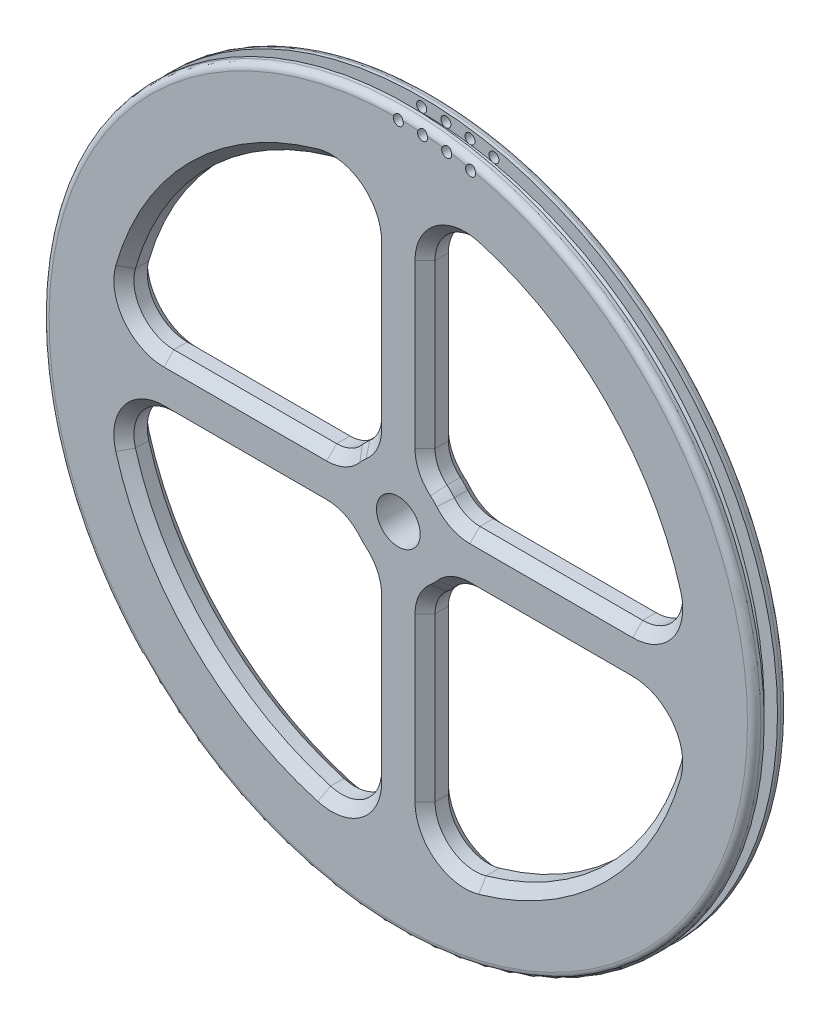
SolidWorks part; units mm, degrees
ref_plane "Front Plane" through (0, 0, 0) normal (0, 0, 1) x (1, 0, 0)
ref_plane "Top Plane" through (0, 0, 0) normal (0, 1, 0) x (1, 0, 0)
ref_plane "Right Plane" through (0, 0, 0) normal (1, 0, 0) x (0, 0, -1)
sketch "Sketch2" plane through (0, 0, 0) normal (0, 0, 1) x (1, 0, 0)
  circle A0 centre (0, 0) radius 50.8
  dimension "D1" = 101.6
extrude "Boss-Extrude2" add sketch "Sketch2" along normal blind 2
sketch "Sketch3" plane through (0, 0, 2) normal (0, 0, 1) x (1, 0, 0)
  circle A2 centre (0, 0) radius 53.3
  circle A3 centre (0, 0) radius 53.3
  dimension "D1" = 2.5
extrude "Boss-Extrude3" add sketch "Sketch3" along normal blind 1.5
ref_plane "Plane1" through (0, 0, 1) normal (0, 0, -1) x (-1, 0, 0)
mirror "Mirror2" about plane through (0, 0, 1) normal (0, 0, -1) of "Boss-Extrude3"
chamfer "Chamfer1" distance 0.5 angle 45 2 edges at (50.8, 0, 0) (50.8, 0, 2)
sketch "Sketch4" plane through (0, 0, -1.5) normal (0, 0, -1) x (-1, 0, 0)
  line L0 (0, 0) -> (0, 4)
  line L1 (0, 0) -> (4, 0)
  line L2 (0, 0) -> (0, -4)
  line L3 (0, 0) -> (-4, 0)
  line L6 (8.0623, -4) -> (42.5, -4)
  line L7 (-4, -8.0623) -> (-4, -42.5)
  line L8 (-8.0623, -4) -> (-42.5, -4)
  line L11 (4, -8.0623) -> (4, -42.5)
  line L12 (0, 0) -> (-42.5, 0) construction
  line L13 (-8.0623, 4) -> (-42.5, 4)
  line L15 (-4, 8.0623) -> (-4, 42.5)
  line L19 (4, 8.0623) -> (4, 42.5)
  line L21 (8.0623, 4) -> (42.5, 4)
  line L24 (0, 0) -> (42.5, 0) construction
  line L25 (4, 0) -> (4, -42.5) construction
  line L26 (0, -4) -> (42.5, -4) construction
  line L28 (0, 0) -> (0, -42.5) construction
  line L29 (0, -4) -> (-42.5, -4) construction
  line L30 (-4, 0) -> (-4, -42.5) construction
  circle A0 centre (0, 0) radius 3.275
  arc A1 (-8.0623, -4) -> (-4, -8.0623) centre (0, 0) ccw
  arc A2 (-42.3113, -4) -> (-4, -42.3113) centre (0, 0) ccw
  arc A3 (4, -8.0623) -> (8.0623, -4) centre (0, 0) ccw
  arc A4 (8.0623, 4) -> (4, 8.0623) centre (0, 0) ccw
  arc A5 (-4, 8.0623) -> (-8.0623, 4) centre (0, 0) ccw
  arc A6 (42.3113, 4) -> (4, 42.3113) centre (0, 0) ccw
  arc A7 (4, -42.3113) -> (42.3113, -4) centre (0, 0) ccw
  arc A8 (-4, 42.3113) -> (-42.3113, 4) centre (0, 0) ccw
  dimension "D1" = 6.55
  dimension "D2" = 18
  dimension "D3" = 85
  dimension "D4" = 4
  dimension "D5" = 4
extrude "Cut-Extrude1" cut sketch "Sketch4" against normal through all contours L15 A8 L13 A5 | L21 A6 L19 A4 | L11 A7 L6 A3 | L8 A2 L7 A1 | L2 A0 L1 | L1 A0 L0 | L0 A0 L3 | L3 A0 L2
fillet "Fillet1" radius 6 8 edges at (-4, 42.3113, 1) (-42.3113, 4, 1) (-42.3113, -4, 1) (-4, -42.3113, 1) (4, -42.3113, 1) (42.3113, -4, 1) (42.3113, 4, 1) (4, 42.3113, 1)
fillet "Fillet2" radius 5 8 edges at (-4, -8.0623, 1) (-8.0623, -4, 1) (-8.0623, 4, 1) (-4, 8.0623, 1) (8.0623, 4, 1) (4, 8.0623, 1) (4, -8.0623, 1) (8.0623, -4, 1)
chamfer "Chamfer2" distance 1.5 angle 45 64 edges at (-22.9136, 4, 3.5) (-8.6109, 4.4684, 3.5) (-39.8921, 6.385, 3.5) (-6.364, 6.364, 3.5) (-30.052, 30.052, 3.5) (-4.4684, 8.6109, 3.5) (-6.385, 39.8921, 3.5) (-4, 22.9136, 3.5) (4, 22.9136, 3.5) (4.4684, 8.6109, 3.5) (6.385, 39.8921, 3.5) (6.364, 6.364, 3.5) (30.052, 30.052, 3.5) (8.6109, 4.4684, 3.5) (39.8921, 6.385, 3.5) (22.9136, 4, 3.5) (8.6109, -4.4684, 3.5) (22.9136, -4, 3.5) (6.364, -6.364, 3.5) (39.8921, -6.385, 3.5) (4.4684, -8.6109, 3.5) (30.052, -30.052, 3.5) (4, -22.9136, 3.5) (6.385, -39.8921, 3.5) (-4, -22.9136, 3.5) (-4.4684, -8.6109, 3.5) (-6.385, -39.8921, 3.5) (-6.364, -6.364, 3.5) (-30.052, -30.052, 3.5) (-8.6109, -4.4684, 3.5) (-39.8921, -6.385, 3.5) (-22.9136, -4, 3.5) (-4, 22.9136, -1.5) (-4.4684, 8.6109, -1.5) (-6.385, 39.8921, -1.5) (-6.364, 6.364, -1.5) (-30.052, 30.052, -1.5) (-8.6109, 4.4684, -1.5) (-39.8921, 6.385, -1.5) (-22.9136, 4, -1.5) (-4, -22.9136, -1.5) (-4.4684, -8.6109, -1.5) (-6.385, -39.8921, -1.5) (-6.364, -6.364, -1.5) (-30.052, -30.052, -1.5) (-8.6109, -4.4684, -1.5) (-39.8921, -6.385, -1.5) (-22.9136, -4, -1.5) (22.9136, 4, -1.5) (8.6109, 4.4684, -1.5) (39.8921, 6.385, -1.5) (6.364, 6.364, -1.5) (30.052, 30.052, -1.5) (4.4684, 8.6109, -1.5) (6.385, 39.8921, -1.5) (4, 22.9136, -1.5) (4, -22.9136, -1.5) (4.4684, -8.6109, -1.5) (6.385, -39.8921, -1.5) (6.364, -6.364, -1.5) (30.052, -30.052, -1.5) (8.6109, -4.4684, -1.5) (39.8921, -6.385, -1.5) (22.9136, -4, -1.5)
fillet "Fillet3" radius 1 2 edges at (53.3, 0, 3.5) (53.3, 0, -1.5)
sketch "Sketch5" plane through (0, 0, 3.5) normal (0, 0, 1) x (1, 0, 0)
  line L0 (0, 50.8) -> (0, 53.3)
  line L1 (0, 0) -> (0, 52.05) construction
  line L2 (0, 0) -> (3.6308, 51.9232) construction
  circle A0 centre (0, 0) radius 53.3 construction
  circle A1 centre (0, 0) radius 50.8 construction
  circle A2 centre (0, 0) radius 53.3
  circle A3 centre (0, 0) radius 50.8
  circle A4 centre (0, 52.05) radius 0.75
  circle A5 centre (3.6308, 51.9232) radius 0.75
  circle A6 centre (7.244, 51.5435) radius 0.75
  circle A7 centre (10.8218, 50.9126) radius 0.75
  circle M1 centre (0, 0) radius 52.3
  dimension "D1" = 1.5
  dimension "D3" = 4
  dimension "D2" = 4
extrude "Cut-Extrude2" cut sketch "Sketch5" against normal through all contours A6 M1 | A7 M1 | A7 M1 | A6 M1 | A4 | A5
